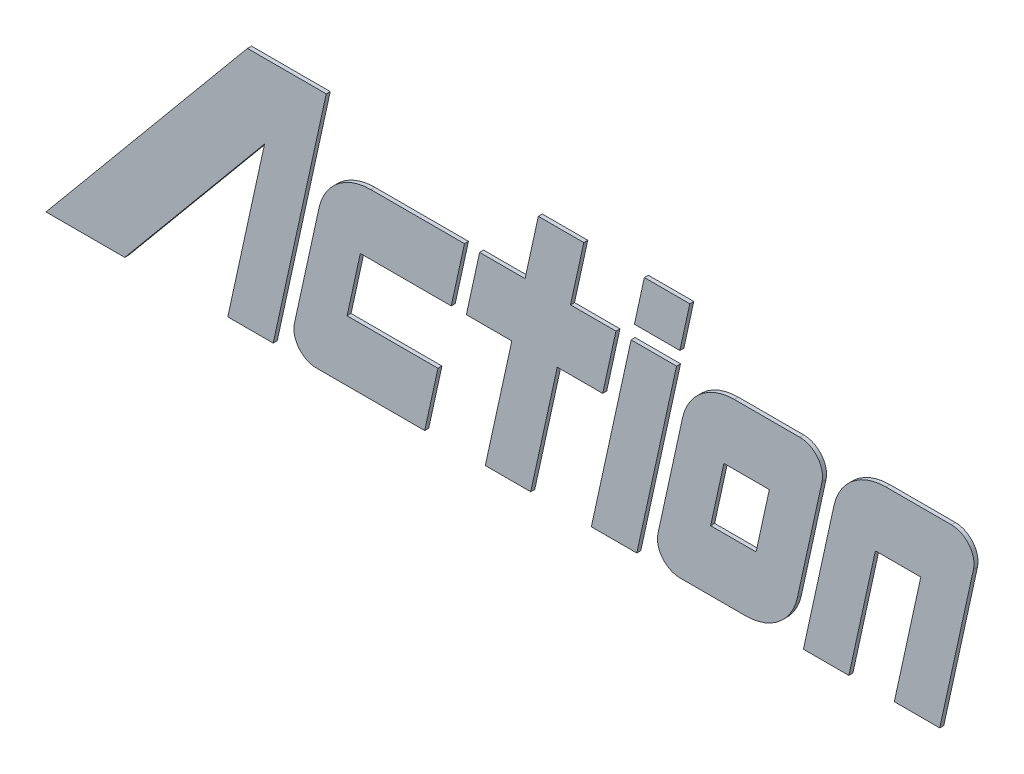
SolidWorks part; units mm, degrees
ref_plane "前视基准面" through (0, 0, 0) normal (0, 0, 1) x (1, 0, 0)
ref_plane "上视基准面" through (0, 0, 0) normal (0, 1, 0) x (1, 0, 0)
ref_plane "右视基准面" through (0, 0, 0) normal (1, 0, 0) x (0, 0, -1)
sketch "Model" plane through (0, 0, 0) normal (0, 0, 1) x (1, 0, 0)
  line L0 (-1192.3171, 979.8509) -> (-1192.6487, 978.3351)
  line L1 (-1191.1803, 979.8509) -> (-1191.5119, 978.3351)
  line L2 (-1189.8629, 980.6768) -> (-1190.4785, 977.8623)
  line L3 (-1201.4116, 979.8509) -> (-1199.138, 979.8509)
  line L4 (-1201.4116, 979.8509) -> (-1201.7432, 978.3351)
  line L5 (-1201.7432, 978.3351) -> (-1199.4696, 978.3351)
  line L6 (-1198.8064, 981.3666) -> (-1199.138, 979.8509)
  line L7 (-1201.1494, 981.3666) -> (-1198.8064, 981.3666)
  line L8 (-1198.4275, 981.3666) -> (-1198.7591, 979.8509)
  line L9 (-1195.0171, 981.3666) -> (-1195.3486, 979.8509)
  line L10 (-1198.4275, 981.3666) -> (-1197.2749, 981.3666)
  line L11 (-1198.7591, 979.8509) -> (-1197.6117, 979.8509)
  line L12 (-1196.1539, 981.3666) -> (-1195.0171, 981.3666)
  line L13 (-1196.4855, 979.8509) -> (-1195.3486, 979.8509)
  line L14 (-1194.6381, 981.3666) -> (-1193.5013, 981.3666)
  line L15 (-1188.2655, 981.3666) -> (-1186.6287, 981.3666)
  line L16 (-1188.5278, 979.8509) -> (-1187.3909, 979.8509)
  line L17 (-1186.0735, 980.6768) -> (-1186.9173, 976.8194)
  line L18 (-1187.3909, 979.8509) -> (-1188.0541, 976.8194)
  line L19 (-1188.5278, 979.8509) -> (-1189.1909, 976.8194)
  line L20 (-1189.5611, 980.3238) -> (-1190.3277, 976.8194)
  line L21 (-1202.2643, 982.8824) -> (-1203.5905, 976.8194)
  line L22 (-1209.2746, 976.8194) -> (-1204.2352, 982.8824)
  line L23 (-1204.7274, 976.8194) -> (-1203.8071, 981.0261)
  line L24 (-1207.3036, 976.8194) -> (-1203.8071, 981.0261)
  line L25 (-1202.445, 980.3238) -> (-1203.0607, 977.5093)
  line L26 (-1199.4696, 978.3351) -> (-1199.8012, 976.8194)
  line L27 (-1197.6223, 979.8509) -> (-1198.2854, 976.8194)
  line L28 (-1196.4855, 979.8509) -> (-1197.1486, 976.8194)
  line L29 (-1194.5552, 981.7456) -> (-1193.4184, 981.7456)
  line L30 (-1193.5013, 981.3666) -> (-1194.496, 976.8194)
  line L31 (-1194.6381, 981.3666) -> (-1195.6328, 976.8194)
  line L32 (-1193.3505, 980.3238) -> (-1193.9662, 977.5093)
  line L33 (-1196.9591, 982.8824) -> (-1197.2907, 981.3666)
  line L34 (-1195.8223, 982.8824) -> (-1196.1539, 981.3666)
  line L35 (-1193.1697, 982.8824) -> (-1193.4184, 981.7456)
  line L36 (-1194.3066, 982.8824) -> (-1194.5552, 981.7456)
  line L37 (-1190.3277, 976.8194) -> (-1189.1909, 976.8194)
  line L38 (-1188.0541, 976.8194) -> (-1186.9173, 976.8194)
  line L39 (-1204.7274, 976.8194) -> (-1203.5905, 976.8194)
  line L40 (-1202.5054, 976.8194) -> (-1199.8012, 976.8194)
  line L41 (-1195.6328, 976.8194) -> (-1194.496, 976.8194)
  line L42 (-1198.2854, 976.8194) -> (-1197.1486, 976.8194)
  line L43 (-1192.3171, 979.8509) -> (-1191.1803, 979.8509)
  line L44 (-1192.0549, 981.3666) -> (-1191.0908, 981.3666)
  line L45 (-1191.0908, 981.3666) -> (-1190.4181, 981.3666)
  line L46 (-1192.6487, 978.3351) -> (-1191.5119, 978.3351)
  line L47 (-1193.4109, 976.8194) -> (-1192.28, 976.8194)
  line L48 (-1192.28, 976.8194) -> (-1191.7742, 976.8194)
  line L49 (-1204.2352, 982.8824) -> (-1202.2643, 982.8824)
  line L50 (-1196.9591, 982.8824) -> (-1195.8223, 982.8824)
  line L51 (-1194.3066, 982.8824) -> (-1193.1697, 982.8824)
  line L52 (-1209.2746, 976.8194) -> (-1207.3007, 976.8194)
  line L53 (-1208.1378, 976.8194) -> (-1207.3036, 976.8194)
  arc A0 (-1201.1494, 981.3666) -> (-1202.445, 980.3238) centre (-1201.1494, 980.0404) ccw
  arc A1 (-1189.8629, 980.6768) -> (-1190.4181, 981.3666) centre (-1190.4181, 980.7982) ccw
  arc A2 (-1192.0549, 981.3666) -> (-1193.3505, 980.3238) centre (-1192.0549, 980.0404) ccw
  arc A3 (-1188.2655, 981.3666) -> (-1189.5611, 980.3238) centre (-1188.2655, 980.0404) ccw
  arc A4 (-1186.0735, 980.6768) -> (-1186.6287, 981.3666) centre (-1186.6287, 980.7982) ccw
  arc A5 (-1191.7742, 976.8194) -> (-1190.4785, 977.8623) centre (-1191.7742, 978.1457) ccw
  arc A6 (-1203.0607, 977.5093) -> (-1202.5054, 976.8194) centre (-1202.5054, 977.3878) ccw
  arc A7 (-1193.9662, 977.5093) -> (-1193.4109, 976.8194) centre (-1193.4109, 977.3878) ccw
extrude "凸台-拉伸1" add sketch "Model" along normal blind 0.1
